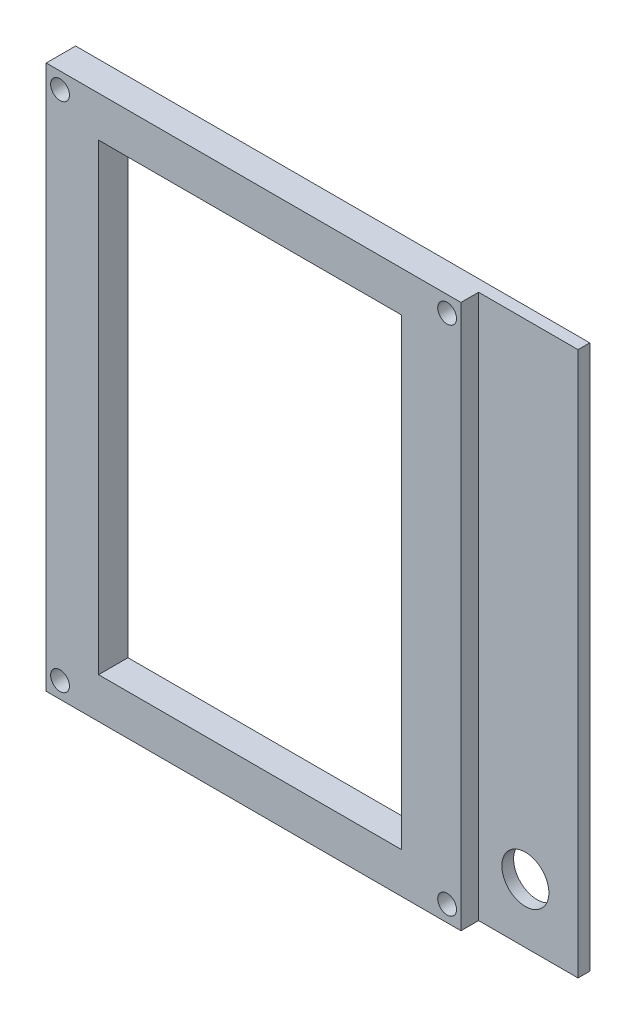
SolidWorks part; units mm, degrees
material "PBT Общее назначение"
ref_plane "Спереди" through (0, 0, 0) normal (0, 0, 1) x (1, 0, 0)
ref_plane "Сверху" through (0, 0, 0) normal (0, 1, 0) x (1, 0, 0)
ref_plane "Справа" through (0, 0, 0) normal (1, 0, 0) x (0, 0, -1)
sketch "Эскиз1" plane through (0, 0, 92.6623) normal (0, 0, -1) x (-1, 0, 0)
  line L4 (-4, 97.5) -> (-75, 97.5)
  line L5 (-75, 97.5) -> (-75, 4.5)
  line L6 (-75, 4.5) -> (-4, 4.5)
  line L7 (-4, 4.5) -> (-4, 97.5)
  line L8 (-4, 97.5) -> (-75, 97.5)
  line L9 (-75, 97.5) -> (-75, 4.5)
  line L10 (-75, 4.5) -> (-4, 4.5)
  line L11 (-4, 4.5) -> (-4, 97.5)
  line L12 (-13.4, 90.1) -> (-64.4, 90.1)
  line L13 (-64.4, 90.1) -> (-64.4, 11.9)
  line L14 (-64.4, 11.9) -> (-13.4, 11.9)
  line L15 (-13.4, 11.9) -> (-13.4, 90.1)
  line L16 (-13.4, 90.1) -> (-64.4, 90.1)
  line L17 (-64.4, 90.1) -> (-64.4, 11.9)
  line L18 (-64.4, 11.9) -> (-13.4, 11.9)
  line L19 (-13.4, 11.9) -> (-13.4, 90.1)
  circle A0 centre (-6.6, 7.5) radius 1.6 construction
  circle A1 centre (-6.6, 7.5) radius 1.6
  circle A2 centre (-72.4, 7.5) radius 1.6 construction
  circle A3 centre (-72.4, 7.5) radius 1.6
  circle A4 centre (-6.6, 94.5) radius 1.6 construction
  circle A5 centre (-6.6, 94.5) radius 1.6
  circle A6 centre (-72.4, 94.5) radius 1.6 construction
  circle A7 centre (-72.4, 94.5) radius 1.6
  dimension "D1" = 0
  dimension "D2" = 0
extrude "Бобышка-Вытянуть1" add sketch "Эскиз1" along normal blind 5
sketch "Эскиз2" plane through (0, 0, 92.6623) normal (0, 0, 1) x (1, 0, 0)
  line L0 (4.25, 97.25) -> (74.75, 97.25)
  line L1 (4.25, 97.25) -> (4.25, 4.75)
  line L2 (74.75, 97.25) -> (74.75, 4.75)
  line L3 (4.25, 4.75) -> (74.75, 4.75)
  line L4 (75, 97.5) -> (75, 4.5) construction
  line L5 (75, 4.5) -> (4, 4.5) construction
  line L6 (4, 4.5) -> (4, 97.5) construction
  line L7 (4, 97.5) -> (75, 97.5) construction
  line L12 (4, 97.5) -> (4, 4.5)
  line L13 (4, 4.5) -> (75, 4.5)
  line L14 (75, 4.5) -> (75, 97.5)
  line L15 (75, 97.5) -> (4, 97.5)
  line L16 (4, 97.5) -> (4, 4.5)
  line L17 (4, 4.5) -> (75, 4.5)
  line L18 (75, 4.5) -> (75, 97.5)
  line L19 (75, 97.5) -> (4, 97.5)
  dimension "D1" = 0.25
  dimension "D2" = 0.25
  dimension "D3" = 0.25
  dimension "D4" = 0.25
  dimension "D5" = 0
extrude "Вырез-Вытянуть1" cut sketch "Эскиз2" against normal through all
sketch "Эскиз3" plane through (0, 0, 92.6623) normal (0, 0, 1) x (1, 0, 0)
  line L0 (13.15, 90.35) -> (64.65, 90.35)
  line L1 (13.15, 90.35) -> (13.15, 11.65)
  line L2 (64.65, 90.35) -> (64.65, 11.65)
  line L3 (13.15, 11.65) -> (64.65, 11.65)
  line L4 (13.4, 90.1) -> (64.4, 90.1) construction
  line L5 (13.4, 11.9) -> (13.4, 90.1) construction
  line L6 (64.4, 90.1) -> (64.4, 11.9) construction
  line L7 (64.4, 11.9) -> (13.4, 11.9) construction
  line L8 (64.4, 11.9) -> (13.4, 11.9)
  line L9 (13.4, 11.9) -> (13.4, 90.1)
  line L10 (64.4, 90.1) -> (64.4, 11.9)
  line L11 (13.4, 90.1) -> (64.4, 90.1)
  dimension "D1" = 0.25
  dimension "D2" = 0.25
  dimension "D3" = 0.25
  dimension "D4" = 0.25
extrude "Вырез-Вытянуть2" cut sketch "Эскиз3" against normal through all
sketch "Эскиз5" plane through (0, 0, 87.6623) normal (0, 0, -1) x (-1, 0, 0)
  line L0 (-64.65, 97.25) -> (-64.65, 4.75)
  line L1 (-64.65, 97.25) -> (-91.65, 97.25)
  line L2 (-64.65, 4.75) -> (-91.65, 4.75)
  line L3 (-91.65, 97.25) -> (-91.65, 4.75)
  line L4 (-74.75, 97.25) -> (-4.25, 97.25) construction
  line L5 (-4.25, 4.75) -> (-74.75, 4.75) construction
  line L6 (-64.65, 11.65) -> (-64.65, 90.35) construction
  circle A0 centre (-72.4, 94.5) radius 1.6 construction
  circle A1 centre (-72.4, 7.5) radius 1.6 construction
  circle A2 centre (-72.4, 94.5) radius 1.6
  circle A3 centre (-72.4, 7.5) radius 1.6
  dimension "D1" = 27
extrude "Бобышка-Вытянуть3" add sketch "Эскиз5" against normal blind 2
sketch "Эскиз7" plane through (0, 0, 87.6623) normal (0, 0, -1) x (-1, 0, 0)
  circle A0 centre (-82.7, 14.8) radius 3.35 construction
  circle A1 centre (-82.7, 14.8) radius 3.35 construction
  circle A2 centre (-82.7, 14.8) radius 4
  dimension "D1" = 8
extrude "Вырез-Вытянуть3" cut sketch "Эскиз7" against normal through all
